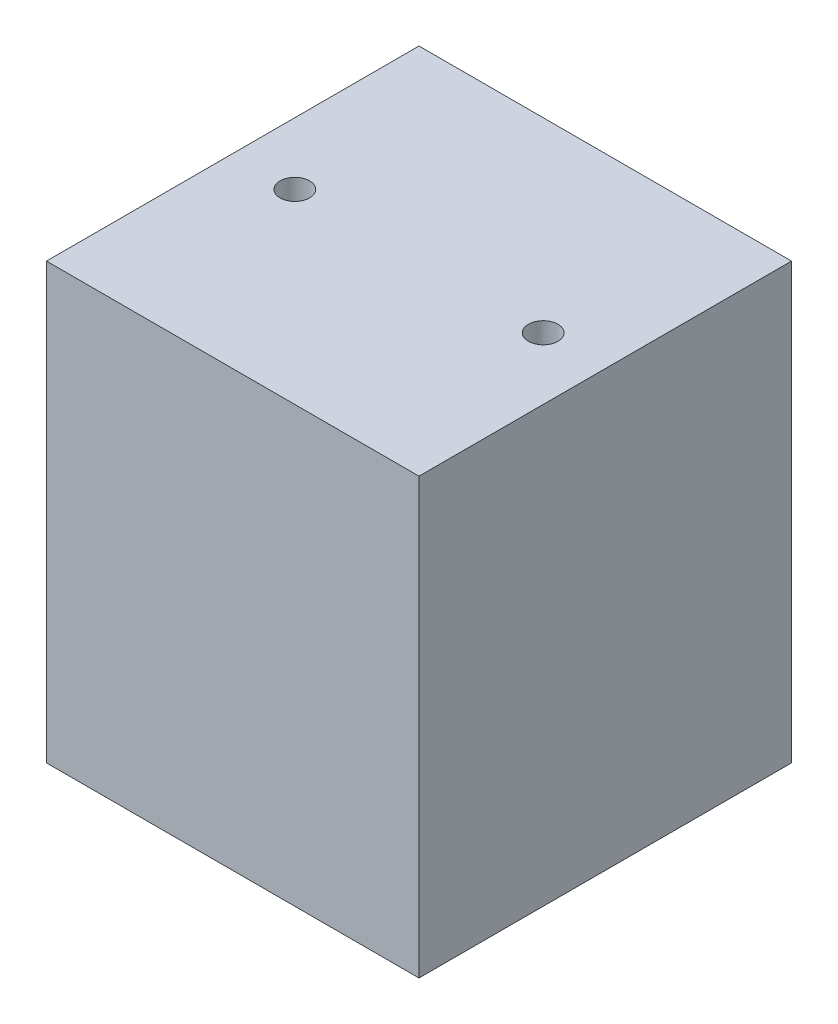
SolidWorks part; units mm, degrees
ref_plane "Front" through (0, 0, 0) normal (0, 0, 1) x (1, 0, 0)
ref_plane "Top" through (0, 0, 0) normal (0, 1, 0) x (1, 0, 0)
ref_plane "Right" through (0, 0, 0) normal (1, 0, 0) x (0, 0, -1)
sketch "Sketch1" plane through (0, 0, 0) normal (0, 1, 0) x (1, 0, 0)
  line L1 (0, 0) -> (60, 0)
  line L2 (0, 0) -> (0, 60)
  line L3 (0, 60) -> (60, 60)
  line L4 (60, 0) -> (60, 60)
extrude "Boss-Extrude1" add sketch "Sketch1" along normal blind 70
sketch "Sketch2" plane through (0, 0, 0) normal (0, -1, 0) x (1, 0, 0)
  line L0 (0, -60) -> (0, 0) construction
  line L1 (0, 0) -> (60, 0) construction
  circle A0 centre (10, -30) radius 2.3815
  circle A1 centre (50, -30) radius 2.3815
  point P4 (0, -30)
  dimension "D1" = 40
  dimension "D2" = 10
  dimension "D3" = 30
extrude "Cut-Extrude1" cut sketch "Sketch2" against normal through all
sketch "Sketch5" plane through (0, 0, 0) normal (0, -1, 0) x (1, 0, 0)
  line L0 (0, 0) -> (60, 0) construction
  circle A0 centre (30, -10) radius 1.9105
  circle A1 centre (30, -50) radius 2.3572
  dimension "D1" = 40
  dimension "D2" = 10
hole_wizard "1/4-20 Tapped Hole1" positions "3DSketch4" profile "Sketch7" tap size "1/4-20" standard "ANSI Inch"
sketch3d "3DSketch4"
  point P0 (30, 0, -10)
  point P3 (30, 0, -50)
cosmetic thread "Hole Thread1" parameters "D2"=6.35
cosmetic thread "Hole Thread2" parameters "D2"=6.35
sketch "Sketch7" plane through (30, 0, -10) normal (1, 0, 0) x (0, 0, -1)
  line L0 (0, 0) -> (0, 20.5838)
  line L1 (0, 20.5838) -> (2.5527, 19.05)
  line L2 (2.5527, 19.05) -> (2.5527, 0)
  line L5 (2.5527, 0) -> (0, 0)
  line L10 (0, 20.5838) -> (-2.5527, 19.05) construction
  line L11 (0, -6.35) -> (0, 107.95) construction
  dimension "Tap Drill Dia." = 5.1054
  dimension "Tap Drill Depth" = 19.05
  dimension "Drill Angle" = 118
